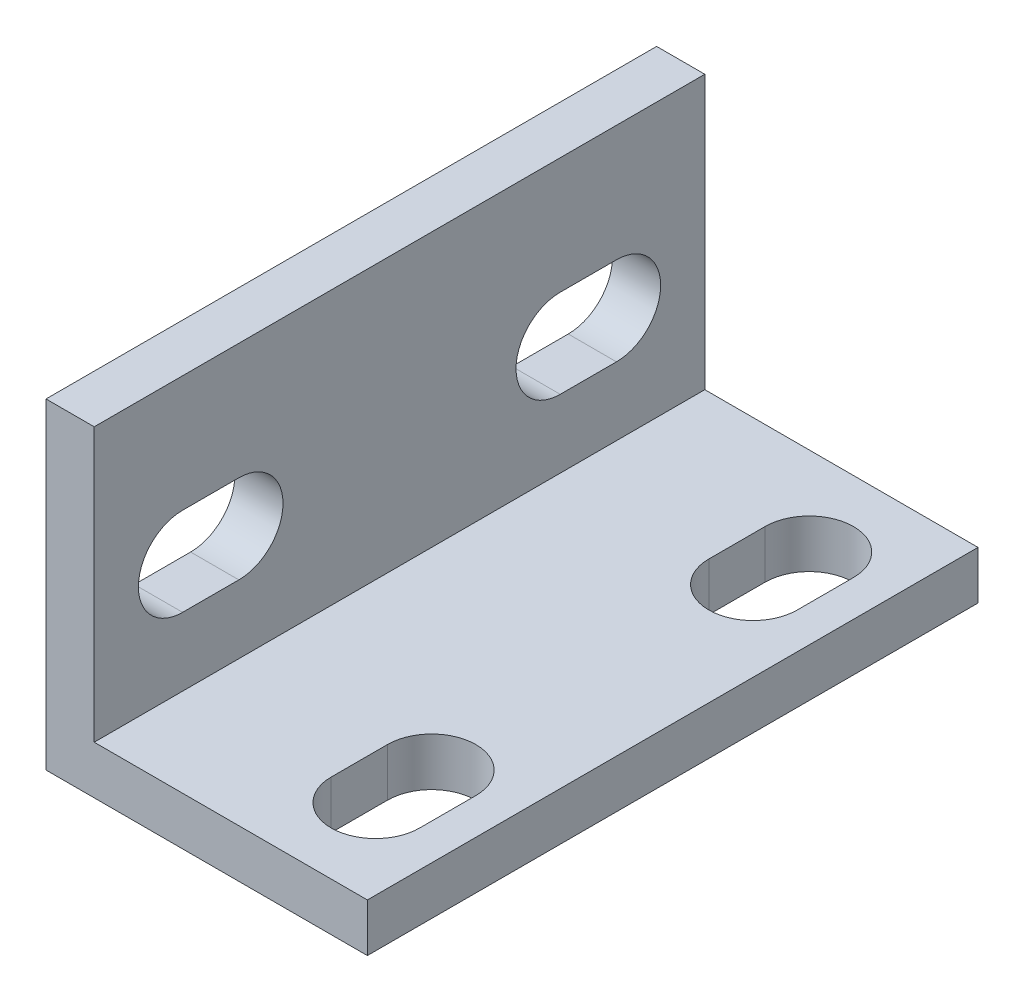
SolidWorks part; units mm, degrees
material "6061-T6 (SS)"
ref_plane "Front Plane" through (0, 0, 0) normal (0, 0, 1) x (1, 0, 0)
ref_plane "Top Plane" through (0, 0, 0) normal (0, 1, 0) x (1, 0, 0)
ref_plane "Right Plane" through (0, 0, 0) normal (1, 0, 0) x (0, 0, -1)
sketch "Sketch1" plane through (0, 0, 0) normal (0, 0, 1) x (1, 0, 0)
  line L0 (0, 20) -> (0, 0)
  line L1 (0, 0) -> (20, 0)
  dimension "D1" = 20
extrude "Extrude-Thin1" add sketch "Sketch1" along normal blind 38 thin thin type one direction reverse wall 3
sketch "Sketch2" plane through (3, 0, 0) normal (1, 0, 0) x (0, 0, -1)
  line L0 (-19, 20) -> (-19, 3) construction
  line L1 (-38, 20) -> (0, 20) construction
  line L2 (-38, 3) -> (0, 3) construction
  line L3 (-29, 10) -> (-32.5, 10) construction
  line L4 (-29, 7.25) -> (-32.5, 7.25)
  line L5 (-29, 12.75) -> (-32.5, 12.75)
  line L6 (-9, 10) -> (-5.5, 10) construction
  line L7 (-9, 7.25) -> (-5.5, 7.25)
  line L8 (-38, 3) -> (0, 3) construction
  line L9 (-9, 12.75) -> (-5.5, 12.75)
  arc A0 (-29, 7.25) -> (-29, 12.75) centre (-29, 10) ccw
  arc A1 (-32.5, 12.75) -> (-32.5, 7.25) centre (-32.5, 10) ccw
  arc A2 (-9, 7.25) -> (-9, 12.75) centre (-9, 10) cw
  arc A3 (-5.5, 12.75) -> (-5.5, 7.25) centre (-5.5, 10) cw
  point P8 (-30.75, 10)
  point P15 (-7.25, 10)
  dimension "D1" = 3.5
  dimension "D2" = 5.5
  dimension "D3" = 7
  dimension "D4" = 23.5
extrude "Cut-Extrude1" cut sketch "Sketch2" against normal through all
sketch "Sketch3" plane through (0, 3, 0) normal (0, 1, 0) x (1, 0, 0)
  line L0 (20, -19) -> (3, -19) construction
  line L1 (20, -38) -> (20, 0) construction
  line L2 (3, -38) -> (3, 0) construction
  line L3 (15, -32.5) -> (15, -29) construction
  line L4 (12.25, -32.5) -> (12.25, -29)
  line L5 (17.75, -32.5) -> (17.75, -29)
  line L6 (15, -5.5) -> (15, -9) construction
  line L7 (12.25, -5.5) -> (12.25, -9)
  line L8 (17.75, -5.5) -> (17.75, -9)
  arc A0 (12.25, -32.5) -> (17.75, -32.5) centre (15, -32.5) ccw
  arc A1 (17.75, -29) -> (12.25, -29) centre (15, -29) ccw
  arc A2 (12.25, -5.5) -> (17.75, -5.5) centre (15, -5.5) cw
  arc A3 (17.75, -9) -> (12.25, -9) centre (15, -9) cw
  point P8 (15, -30.75)
  point P15 (15, -7.25)
  dimension "D1" = 3.5
  dimension "D2" = 5.5
  dimension "D3" = 12
  dimension "D4" = 23.5
extrude "Cut-Extrude2" cut sketch "Sketch3" against normal through all
